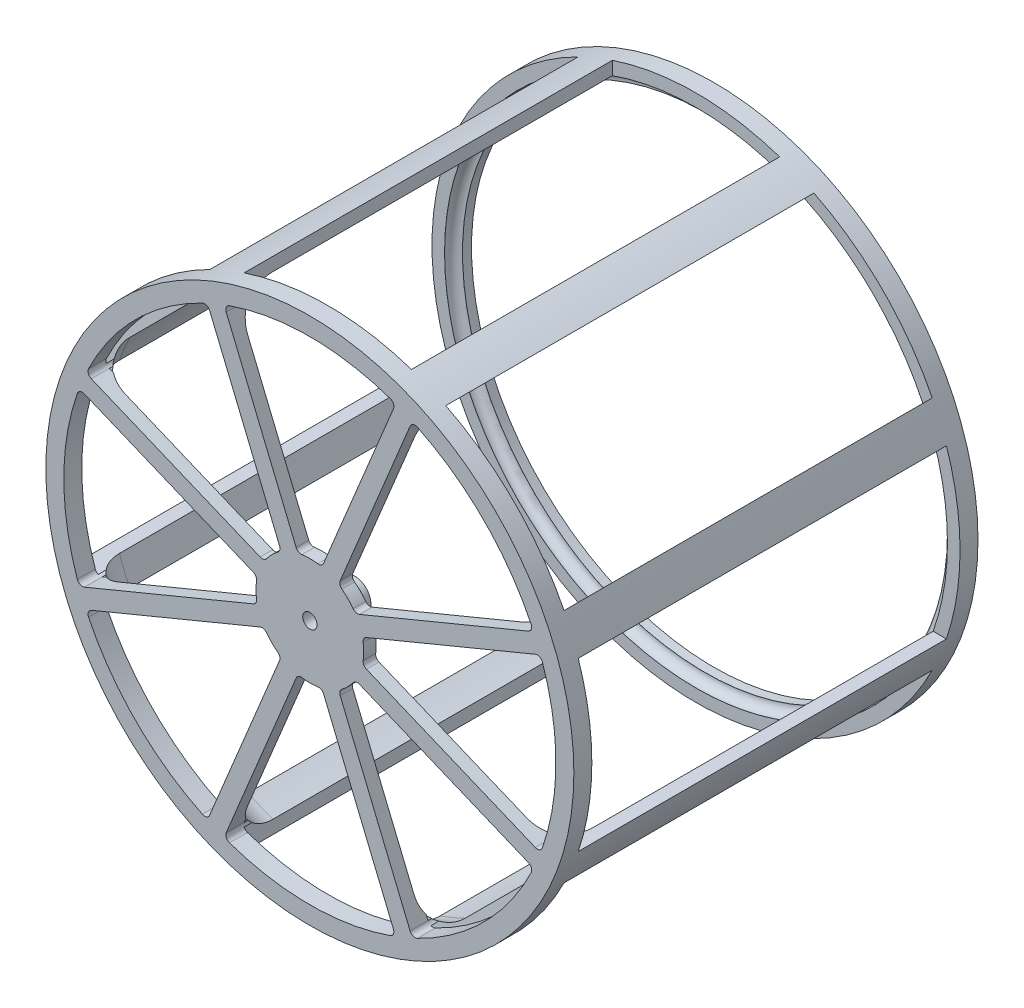
SolidWorks part; units mm, degrees
ref_plane "Front Plane" through (0, 0, 0) normal (0, 0, 1) x (1, 0, 0)
ref_plane "Top Plane" through (0, 0, 0) normal (0, 1, 0) x (1, 0, 0)
ref_plane "Right Plane" through (0, 0, 0) normal (1, 0, 0) x (0, 0, -1)
sketch "Sketch1" plane through (0, 0, 0) normal (1, 0, 0) x (0, 0, -1)
  line L0 (0, 0) -> (46.6464, 0) construction
  line L1 (1.778, 6.096) -> (1.778, 30.734)
  line L2 (57.15, 37.338) -> (0, 37.338)
  line L3 (0, 1.016) -> (0, 37.338)
  line L4 (54.6354, 35.56) -> (6.604, 35.56)
  line L5 (0, 1.016) -> (6.35, 1.016)
  line L6 (6.35, 1.016) -> (6.35, 2.286)
  line L7 (6.35, 2.286) -> (5.588, 2.286)
  line L8 (57.15, 37.338) -> (57.15, 34.29)
  line L9 (0, 3.7177) -> (0, 37.338) construction
  line L10 (0, 3.7177) -> (-5.2526, 1.8207) construction
  line L11 (57.15, 35.56) -> (1.778, 35.56) construction
  line L12 (1.778, 2.4695) -> (1.778, 35.56) construction
  line L13 (55.88, 34.3154) -> (55.88, 34.29)
  line L14 (1.778, 2.4695) -> (-4.6486, 0.1484) construction
  line L15 (55.88, 34.29) -> (57.15, 34.29)
  arc A0 (1.778, 6.096) -> (5.588, 2.286) centre (5.588, 6.096) ccw
  arc A1 (6.604, 35.56) -> (1.778, 30.734) centre (6.604, 30.734) ccw
  arc A2 (54.6354, 35.56) -> (55.88, 34.3154) centre (54.6354, 34.3154) cw
  point P25 (55.88, 35.56)
  dimension "D5" = 1.27
  dimension "D6" = 4.826
  dimension "D8" = 3.81
  dimension "D11" = 1.2446
  dimension "D1" = 2.032
  dimension "D2" = 71.12
  dimension "D3" = 1.778
  dimension "D4" = 6.35
  dimension "D7" = 57.15
  dimension "D9" = 1.27
  dimension "D10" = 1.27
revolve "Revolve1" add sketch "Sketch1" angle 360 about L0
sketch "Sketch3" plane through (0, 0, 0) normal (0, 0, 1) x (1, 0, 0)
  line L0 (0, 0) -> (14.7444, 35.5961) construction
  line L1 (0, 0) -> (-14.9584, 36.1127) construction
  line L2 (0, 0) -> (0, 50.266) construction
  line L3 (1.9386, 7.999) -> (11.8285, 31.8751)
  line L4 (-1.9386, 7.999) -> (-11.8285, 31.8751)
  arc A0 (-1.1224, 7.5369) -> (1.1224, 7.5369) centre (0, 0) cw
  arc A1 (-11.3735, 32.8868) -> (11.3735, 32.8868) centre (0, 0) cw
  circle A2 centre (0, 0) radius 37.338 construction
  arc A3 (11.8285, 31.8751) -> (11.3735, 32.8868) centre (11.1245, 32.1667) ccw
  arc A4 (-11.3735, 32.8868) -> (-11.8285, 31.8751) centre (-11.1245, 32.1667) ccw
  arc A5 (1.9386, 7.999) -> (1.1224, 7.5369) centre (1.2346, 8.2906) cw
  arc A6 (-1.9386, 7.999) -> (-1.1224, 7.5369) centre (-1.2346, 8.2906) ccw
  dimension "D3" = 2.54
  dimension "D4" = 7.62
  dimension "D5" = 2.54
  dimension "D6" = 0.762
  dimension "D1" = 22.5
  dimension "D2" = 45
extrude "Spoke" cut sketch "Sketch3" against normal blind 7.62
sketch "Sketch4" plane through (0, 0, 0) normal (0, 1, 0) x (1, 0, 0)
  line L0 (37.338, 57.15) -> (-37.338, 57.15) construction
  line L1 (-11.8285, 2.54) -> (11.8285, 2.54)
  line L2 (-11.8285, 2.54) -> (-11.8285, 54.61)
  line L3 (-11.8285, 54.61) -> (11.8285, 54.61)
  line L4 (11.8285, 2.54) -> (11.8285, 54.61)
  line L5 (-11.8285, 2.54) -> (11.8285, 54.61) construction
  line L6 (-11.8285, 54.61) -> (11.8285, 2.54) construction
  point P4 (0, 28.575)
  dimension "D1" = 2.54
  dimension "D2" = 2.54
extrude "Tread" cut sketch "Sketch4" along normal through all from offset 15.24
pattern_circular "CirPattern1" count 8 over 360 about axis through (0, 0, 0) along (0, 0, 1) of "Tread", "Spoke"
